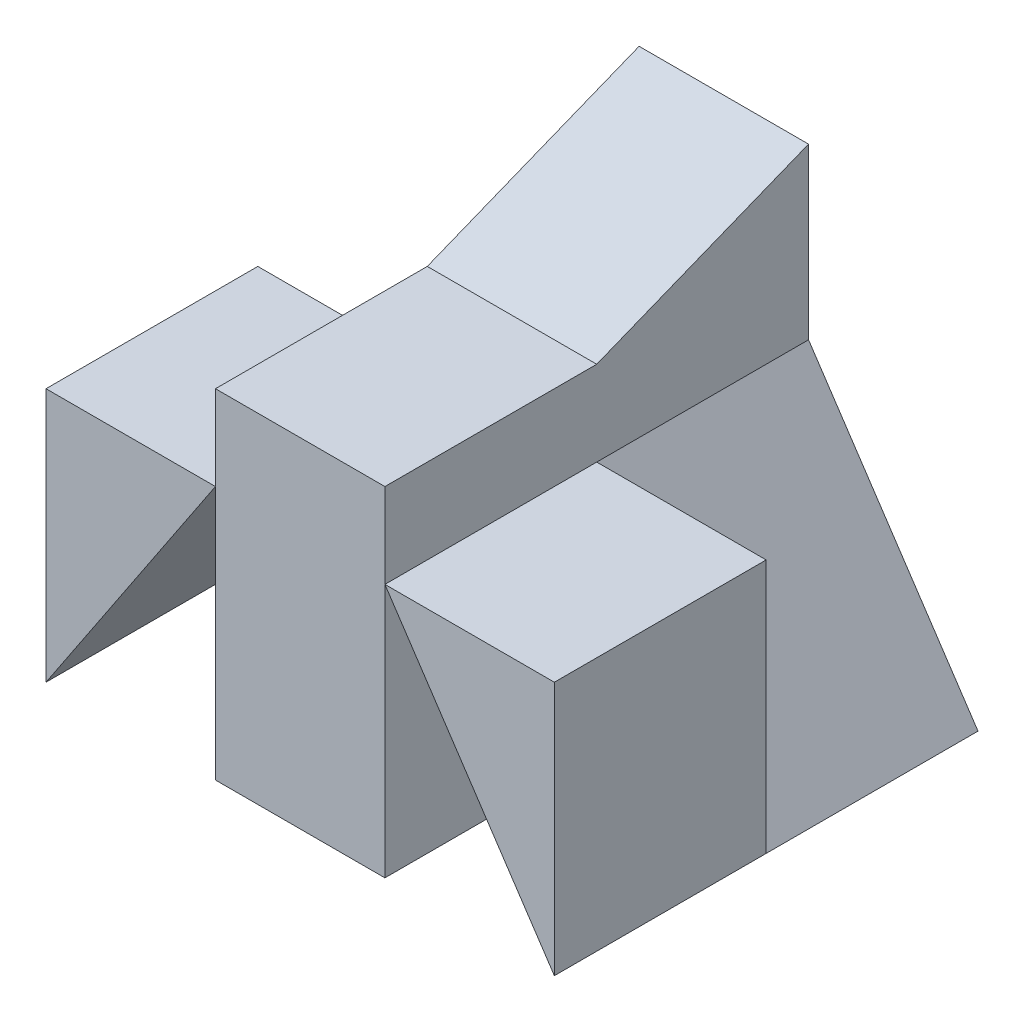
SolidWorks part; units mm, degrees
ref_plane "Front Plane" through (0, 0, 0) normal (0, 0, 1) x (1, 0, 0)
ref_plane "Top Plane" through (0, 0, 0) normal (0, 1, 0) x (1, 0, 0)
ref_plane "Right Plane" through (0, 0, 0) normal (1, 0, 0) x (0, 0, -1)
sketch "Sketch1" plane through (0, 0, 0) normal (0, 0, 1) x (1, 0, 0)
  line L1 (0, 0) -> (6, 0)
  line L2 (0, 0) -> (0, 3)
  line L3 (0, 3) -> (6, 3)
  line L4 (6, 0) -> (6, 3)
  line L5 (2, 3) -> (4, 3)
  line L6 (2, 3) -> (2, 5)
  line L7 (2, 5) -> (4, 5)
  line L8 (4, 3) -> (4, 5)
  dimension "D1" = 3
  dimension "D2" = 6
  dimension "D3" = 2
  dimension "D4" = 2
  dimension "D5" = 2
extrude "Boss-Extrude1" add sketch "Sketch1" along normal blind 5 contours L1 L4 L3 L2 | L3 L8 L7 L6
sketch "Sketch2" plane through (4, 0, 0) normal (1, 0, 0) x (0, 0, -1)
  line L0 (0, 5) -> (-2.5, 4)
  line L1 (-2.5, 4) -> (-5, 4)
  line L2 (-5, 3) -> (-5, 5) construction
  line L3 (-5, 4) -> (-5, 5)
  line L4 (-5, 5) -> (0, 5)
  dimension "D1" = 1
  dimension "D2" = 2.5
extrude "Cut-Extrude2" cut sketch "Sketch2" against normal blind 5
sketch "Sketch8" plane through (0, 0, 0) normal (0, 0, -1) x (-1, 0, 0)
  line L0 (-4, 3) -> (-6, 0)
  line L1 (-6, 0) -> (-6, 3)
  line L2 (-6, 3) -> (-4, 3)
extrude "Cut-Extrude14" cut sketch "Sketch8" against normal blind 2.5
sketch "Sketch9" plane through (0, 0, 5) normal (0, 0, 1) x (1, 0, 0)
  line L0 (4, 3) -> (6, 0)
  line L1 (6, 0) -> (4, 0)
  line L2 (0, 0) -> (6, 0) construction
  line L3 (4, 0) -> (4, 3)
extrude "Cut-Extrude15" cut sketch "Sketch9" against normal blind 2.5
sketch "Sketch10" plane through (0, 0, 5) normal (0, 0, 1) x (1, 0, 0)
  line L0 (2, 3) -> (0, 0)
  line L1 (0, 0) -> (2, 0)
  line L2 (2, 0) -> (2, 3)
sketch "Sketch11" plane through (0, 0, 0) normal (0, 0, -1) x (-1, 0, 0)
  line L0 (0, 3) -> (-2, 3)
  line L1 (-2, 3) -> (0, 0)
  line L2 (0, 0) -> (0, 3)
extrude "Cut-Extrude17" cut sketch "Sketch11" against normal blind 2.5
extrude "Cut-Extrude18" cut sketch "Sketch10" against normal blind 2.5
